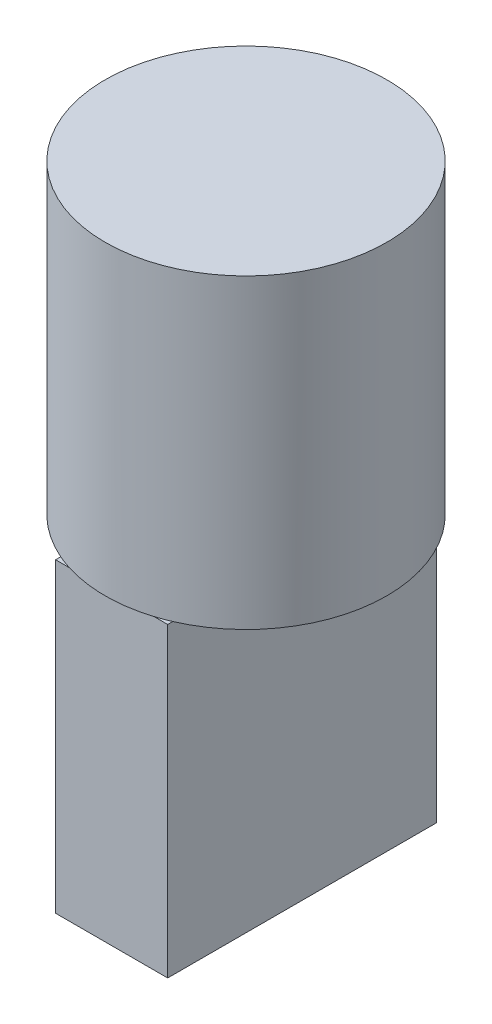
SolidWorks part; units mm, degrees
ref_plane "Спереди" through (0, 0, 0) normal (0, 0, 1) x (1, 0, 0)
ref_plane "Сверху" through (0, 0, 0) normal (0, 1, 0) x (1, 0, 0)
ref_plane "Справа" through (0, 0, 0) normal (1, 0, 0) x (0, 0, -1)
sketch "Эскиз1" plane through (0, 0, 0) normal (0, 1, 0) x (1, 0, 0)
  circle A0 centre (0, 0) radius 19.32
  dimension "D1" = 38.64
extrude "Бобышка-Вытянуть1" add sketch "Эскиз1" along normal blind 42
sketch "Эскиз2" plane through (0, 0, 0) normal (0, -1, 0) x (1, 0, 0)
  line L1 (-7.6876, 18.4288) -> (7.6876, 18.4288)
  line L2 (-7.6876, 18.4288) -> (-7.6876, -18.4288)
  line L3 (-7.6876, -18.4288) -> (7.6876, -18.4288)
  line L4 (7.6876, 18.4288) -> (7.6876, -18.4288)
  line L5 (-7.6876, 18.4288) -> (7.6876, -18.4288) construction
  line L6 (-7.6876, -18.4288) -> (7.6876, 18.4288) construction
  point P0 (0, 0)
extrude "Бобышка-Вытянуть2" add sketch "Эскиз2" along normal blind 42
